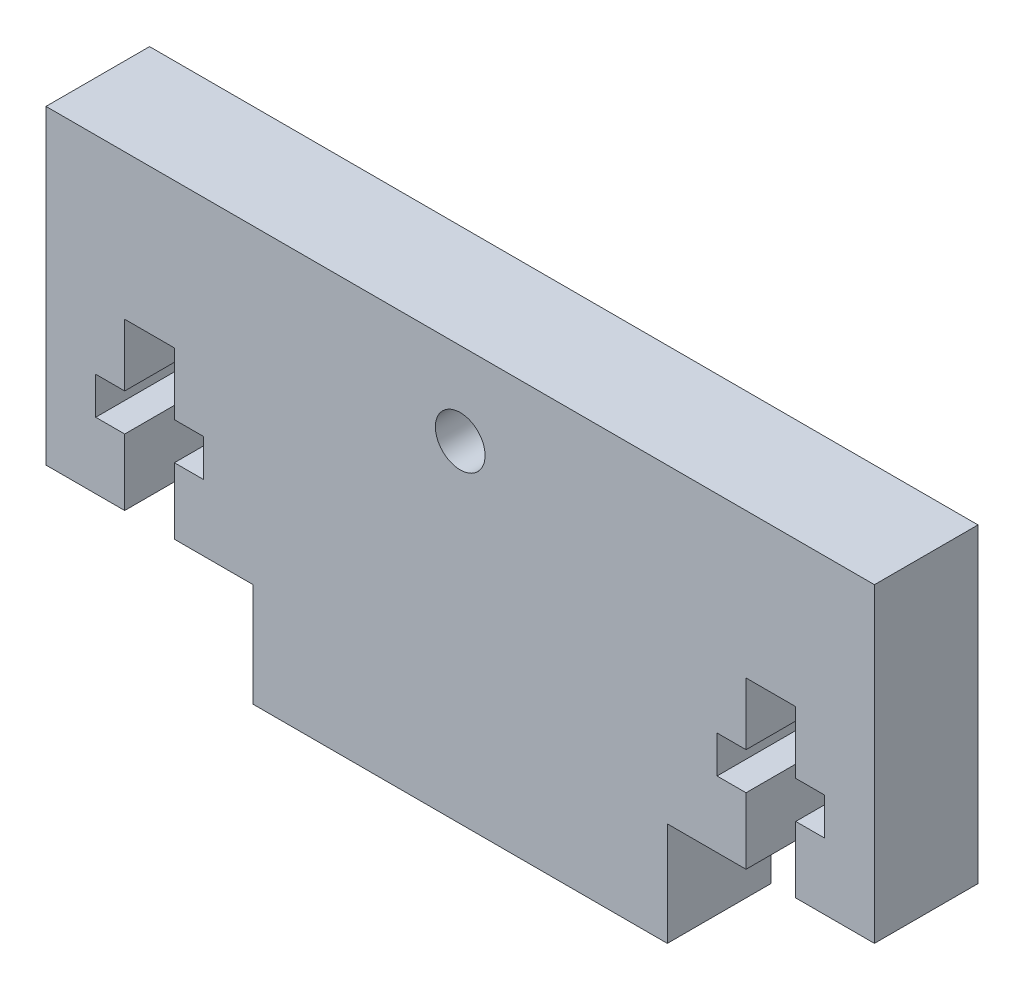
SolidWorks part; units mm, degrees
ref_plane "Front Plane" through (0, 0, 0) normal (0, 0, 1) x (1, 0, 0)
ref_plane "Top Plane" through (0, 0, 0) normal (0, 1, 0) x (1, 0, 0)
ref_plane "Right Plane" through (0, 0, 0) normal (1, 0, 0) x (0, 0, -1)
sketch "Sketch1" plane through (0, 0, 0) normal (0, 0, 1) x (1, 0, 0)
  line L0 (25.4, 25.4) -> (25.4, 0) construction
  line L1 (0, 25.4) -> (50.8, 25.4)
  line L2 (0, 25.4) -> (0, 0)
  line L3 (0, 0) -> (50.8, 0)
  line L4 (50.8, 25.4) -> (50.8, 0)
  line L7 (0, 6.35) -> (12.7, 6.35)
  line L8 (12.7, 0) -> (12.7, 6.35)
  line L11 (50.8, 6.35) -> (38.1, 6.35)
  line L12 (38.1, 0) -> (38.1, 6.35)
  line L14 (42.926, 6.35) -> (42.926, 16.51)
  line L15 (42.926, 16.51) -> (45.974, 16.51)
  line L16 (45.974, 6.35) -> (45.974, 16.51)
  line L17 (41.148, 12.7) -> (47.752, 12.7)
  line L18 (41.148, 12.7) -> (41.148, 10.414)
  line L19 (41.148, 10.414) -> (47.752, 10.414)
  line L20 (47.752, 12.7) -> (47.752, 10.414)
  line L21 (9.652, 10.414) -> (3.048, 10.414)
  line L22 (3.048, 12.7) -> (3.048, 10.414)
  line L23 (9.652, 12.7) -> (3.048, 12.7)
  line L24 (9.652, 12.7) -> (9.652, 10.414)
  line L25 (7.874, 16.51) -> (4.826, 16.51)
  line L26 (4.826, 6.35) -> (4.826, 16.51)
  line L28 (7.874, 6.35) -> (7.874, 16.51)
  point P15 (44.45, 16.51)
  point P20 (41.148, 11.557)
  point P21 (47.752, 11.557)
  point P32 (0, 0)
  dimension "D1" = 50.8
  dimension "D2" = 25.4
  dimension "D3" = 12.7
  dimension "D4" = 6.35
  dimension "D5" = 12.7
  dimension "D6" = 6.35
  dimension "D7" = 10.16
  dimension "D8" = 6.35
  dimension "D9" = 3.048
  dimension "D10" = 2.286
  dimension "D11" = 4.064
  dimension "D12" = 1.778
  dimension "D13" = 1.778
extrude "Boss-Extrude1" add sketch "Sketch1" along normal blind 6.35 contours L0 L1 L2 L7 L26 L21 L22 L23 L25 L28 L24 L8 L3 | L1 L0 L3 L12 L11 L14 L19 L18 L17 L15 L16 L20 L4
sketch "Sketch2" plane through (0, 0, 6.35) normal (0, 0, 1) x (1, 0, 0)
  line L0 (0, 25.4) -> (0, 6.35) construction
  line L1 (0, 25.4) -> (50.8, 25.4) construction
  circle A0 centre (25.4, 20.32) radius 1.524
  dimension "D2" = 3.048
  dimension "D1" = 25.4
  dimension "D3" = 5.08
extrude "Cut-Extrude1" cut sketch "Sketch2" against normal through all
